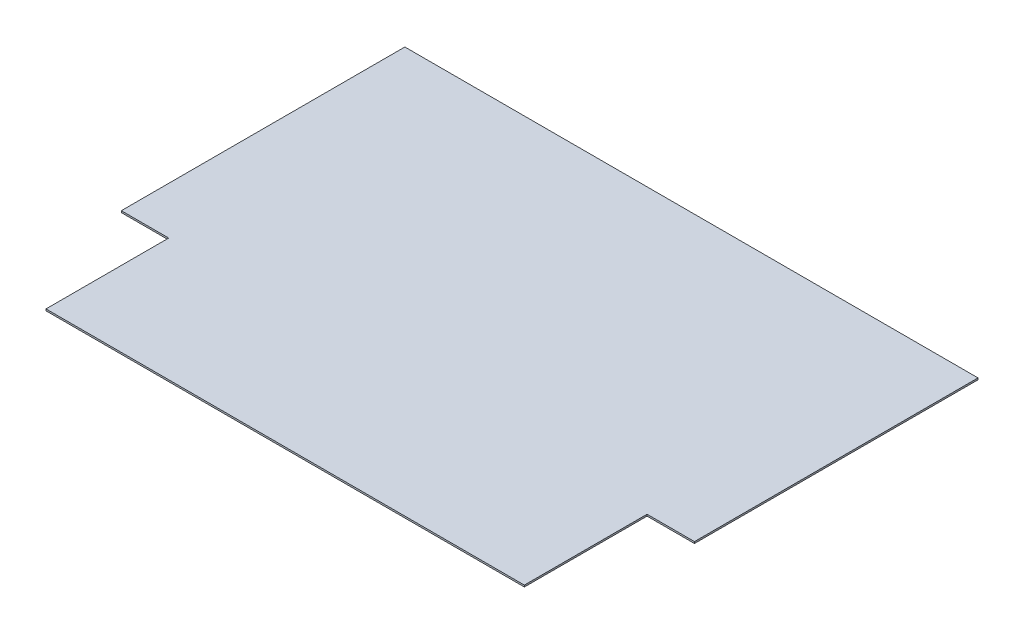
SolidWorks part; units mm, degrees
ref_plane "Front Plane" through (0, 0, 0) normal (0, 0, 1) x (1, 0, 0)
ref_plane "Top Plane" through (0, 0, 0) normal (0, 1, 0) x (1, 0, 0)
ref_plane "Right Plane" through (0, 0, 0) normal (1, 0, 0) x (0, 0, -1)
sketch "Sketch1" plane through (0, 0, 0) normal (0, 1, 0) x (1, 0, 0)
  line L1 (-914.4, 0) -> (914.4, 0)
  line L3 (-914.4, 3048) -> (914.4, 3048)
  line L4 (914.4, 0) -> (914.4, 3048)
  line L5 (-914.4, 0) -> (-1438.8995, 0)
  line L7 (-914.4, 3048) -> (-1438.8995, 3048)
  line L8 (-1438.8995, 0) -> (-1438.8995, 3048)
  point P5 (0, 0)
  dimension "D1" = 3048
  dimension "D2" = 1828.8
extrude "Boss-Extrude1" add sketch "Sketch1" along normal blind 6.35
ref_plane "Plane1" [suppressed] through (0, 0, 0) normal (1, 0, 0) x (0, 0, -1)
sketch "Sketch2" plane through (0, 6.35, 0) normal (0, 1, 0) x (1, 0, 0)
  line L0 (-1438.8995, 3048) -> (-1438.8995, 0) construction
  line L1 (914.4, 0) -> (533.4, 0)
  line L2 (914.4, 0) -> (914.4, 460.375)
  line L3 (711.2, 460.375) -> (533.4, 460.375)
  line L4 (533.4, 0) -> (533.4, 460.375)
  line L5 (914.4, 3048) -> (533.4, 3048)
  line L6 (914.4, 3048) -> (914.4, 2587.625)
  line L8 (533.4, 3048) -> (533.4, 2587.625)
  line L9 (-1261.0995, 460.375) -> (-1438.8995, 460.375)
  line L10 (-1261.0995, 460.375) -> (-1261.0995, 0)
  line L11 (-1261.0995, 0) -> (-1438.8995, 0)
  line L12 (-1438.8995, 460.375) -> (-1438.8995, 0)
  line L13 (-1438.8995, 0) -> (914.4, 0) construction
  line L14 (711.2, 2587.625) -> (533.4, 2587.625)
  line L15 (-1438.8995, 3048) -> (-1261.0995, 3048)
  line L16 (-1438.8995, 3048) -> (-1438.8995, 2587.625)
  line L17 (-1438.8995, 2587.625) -> (-1261.0995, 2587.625)
  line L18 (-1261.0995, 3048) -> (-1261.0995, 2587.625)
  line L20 (711.2, 460.375) -> (711.2, 2587.625)
  line L22 (914.4, 460.375) -> (914.4, 2587.625)
  line L23 (812.165, 2587.625) -> (812.165, 460.375) construction
  line L24 (711.2, 1524) -> (914.4, 1524) construction
  line L25 (914.4, 2587.625) -> (711.2, 2587.625) construction
  line L26 (914.4, 460.375) -> (711.2, 460.375) construction
  line L27 (-1438.8995, 1524) -> (914.4, 1524) construction
  line L28 (914.4, 3048) -> (-1438.8995, 3048) construction
  point P121 (812.165, 1524)
  dimension "D1" = 381
  dimension "D2" = 460.375
  dimension "D3" = 177.8
  dimension "D4" = 177.8
  dimension "D5" = 460.375
  dimension "D6" = 177.8
  dimension "D7" = 460.375
  dimension "D8" = 460.375
extrude "Cut-Extrude1" cut sketch "Sketch2" against normal through all
sketch "Sketch3" plane through (0, 6.35, 0) normal (0, 1, 0) x (1, 0, 0)
  line L0 (-1438.8995, 2587.625) -> (-1438.8995, 460.375) construction
  line L1 (-1438.8995, 1524) -> (711.2, 1524)
  line L2 (-1438.8995, 1524) -> (-1438.8995, 3048)
  line L3 (-1438.8995, 3048) -> (711.2, 3048)
  line L4 (711.2, 1524) -> (711.2, 3048)
  line L5 (-363.8498, 3048) -> (-363.8498, 1524) construction
  line L6 (-1438.8995, 2286) -> (711.2, 2286) construction
  line L7 (533.4, 3048) -> (-1261.0995, 3048) construction
  line L8 (711.2, 2587.625) -> (711.2, 460.375) construction
  point P316 (-363.8498, 2286)
extrude "Cut-Extrude2" cut sketch "Sketch3" against normal through all
equation "\"D5@Sketch2\"=\"D2@Sketch2\""
